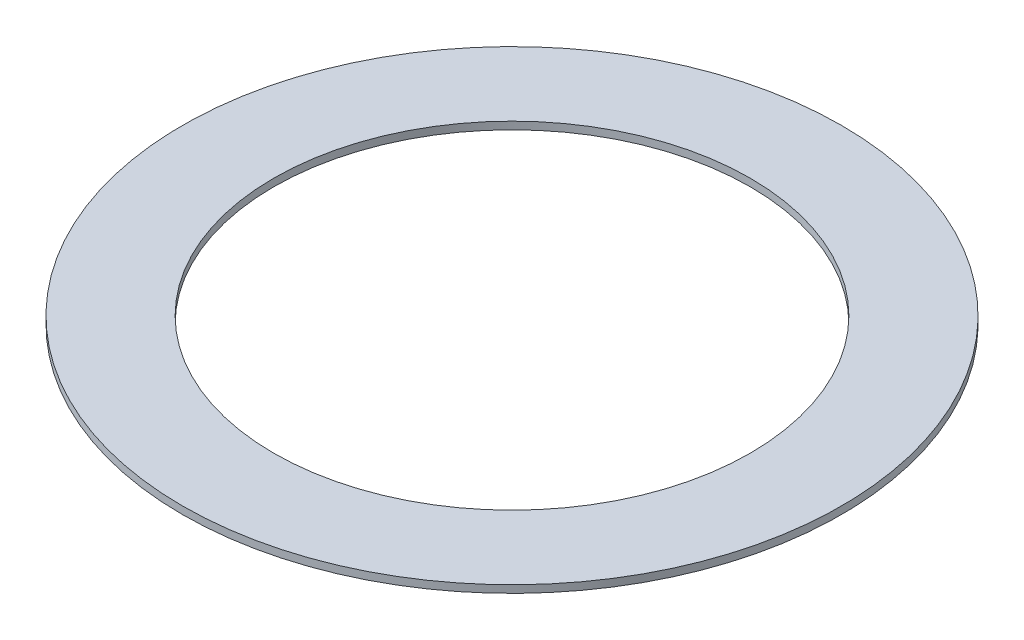
SolidWorks part; units mm, degrees
material "Oak"
ref_plane "Front Plane" through (0, 0, 0) normal (0, 0, 1) x (1, 0, 0)
ref_plane "Top Plane" through (0, 0, 0) normal (0, 1, 0) x (1, 0, 0)
ref_plane "Right Plane" through (0, 0, 0) normal (1, 0, 0) x (0, 0, -1)
sketch "Sketch1" plane through (0, 0, 0) normal (0, 1, 0) x (1, 0, 0)
  circle A0 centre (0, 0) radius 76.2
  circle A1 centre (0, 0) radius 105.41
  dimension "D1" = 152.4
  dimension "D2" = 210.82
extrude "Boss-Extrude1" add sketch "Sketch1" along normal blind 2.4
